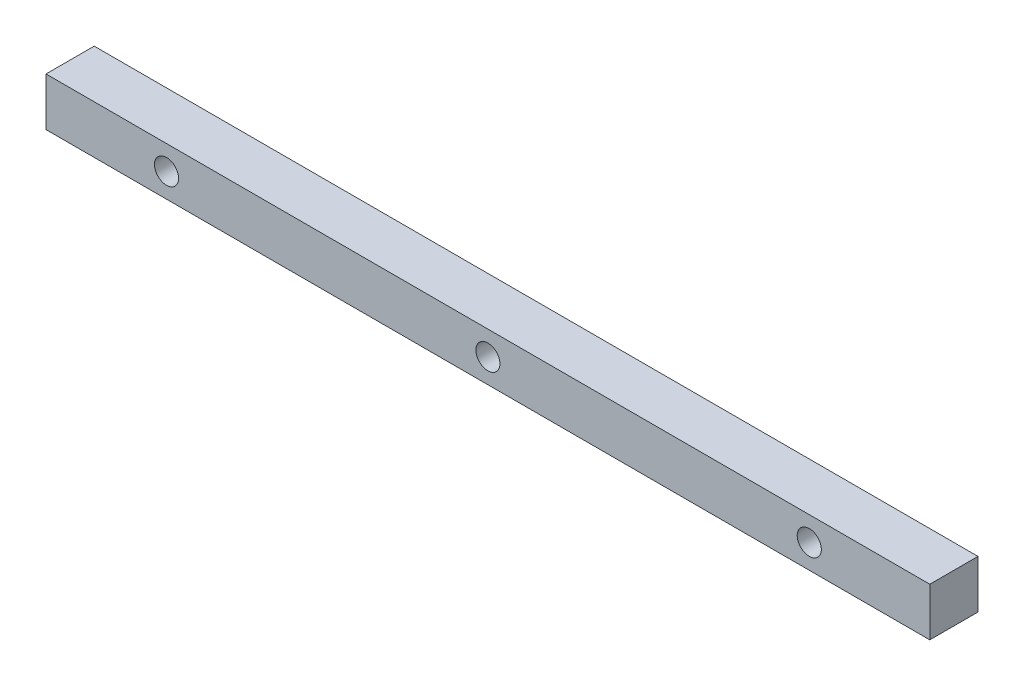
SolidWorks part; units mm, degrees
ref_plane "Plan de face" through (0, 0, 0) normal (0, 0, 1) x (1, 0, 0)
ref_plane "Plan de dessus" through (0, 0, 0) normal (0, 1, 0) x (1, 0, 0)
ref_plane "Plan de droite" through (0, 0, 0) normal (1, 0, 0) x (0, 0, -1)
sketch "Esquisse1" plane through (0, 0, 0) normal (0, 0, 1) x (1, 0, 0)
  line L1 (-45.4029, 16.9903) -> (64.5971, 16.9903)
  line L2 (-45.4029, 16.9903) -> (-45.4029, 10.9903)
  line L3 (-45.4029, 10.9903) -> (64.5971, 10.9903)
  line L4 (64.5971, 16.9903) -> (64.5971, 10.9903)
  dimension "D1" = 110
  dimension "D2" = 6
extrude "Boss.-Extru.1" add sketch "Esquisse1" along normal blind 6
sketch "Esquisse2" plane through (0, 0, 6) normal (0, 0, 1) x (1, 0, 0)
  line L0 (64.5971, 16.9903) -> (-45.4029, 16.9903) construction
  line L1 (-45.4029, 16.9903) -> (-45.4029, 10.9903) construction
  circle A0 centre (-30.4029, 13.9903) radius 1.5
  circle A1 centre (9.5971, 13.9903) radius 1.5
  circle A2 centre (49.5971, 13.9903) radius 1.5
  point P8 (-45.4029, 13.9903)
  point P10 (0, 0)
  dimension "D1" = 3
  dimension "D2" = 3
  dimension "D3" = 3
  dimension "D4" = 3
  dimension "D5" = 3
  dimension "D6" = 3
  dimension "D7" = 40
  dimension "D8" = 40
  dimension "D9" = 15
extrude "Enlèv. mat.-Extru.1" cut sketch "Esquisse2" against normal blind 3
